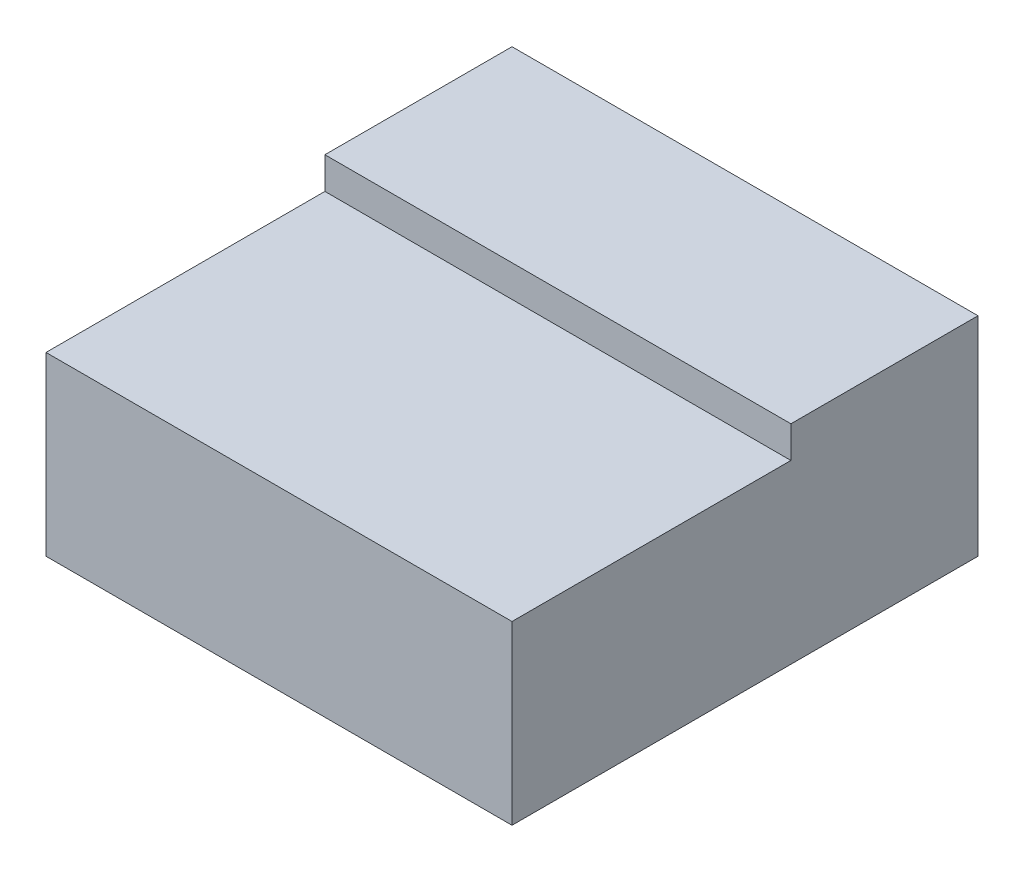
SolidWorks part; units mm, degrees
material "Copper"
ref_plane "Front" through (0, 0, 0) normal (0, 0, 1) x (1, 0, 0)
ref_plane "Top" through (0, 0, 0) normal (0, 1, 0) x (1, 0, 0)
ref_plane "Right" through (0, 0, 0) normal (1, 0, 0) x (0, 0, -1)
sketch "Sketch3" plane through (0, 0, 0) normal (1, 0, 0) x (0, 0, -1)
  line L1 (0, 0) -> (13.2, 0)
  line L2 (0, 0) -> (0, 5)
  line L3 (0, 5) -> (7.9, 5)
  line L4 (13.2, 0) -> (13.2, 5)
  line L6 (13.2, 5) -> (13.2, 5.9)
  line L7 (13.2, 5.9) -> (7.9, 5.9)
  line L8 (7.9, 5) -> (7.9, 5.9)
  point P8 (8.738, 5)
  dimension "D1" = 5
  dimension "D2" = 13.2
  dimension "D3" = 0.9
  dimension "D4" = 5.3
extrude "Boss-Extrude1" add sketch "Sketch3" along normal blind 13.2
hole_wizard "Ø1.5mm Dowel Hole1" positions "Sketch8" profile "Sketch7" hole size "Ø1.5" standard "ANSI Metric"
sketch "Sketch8" plane through (0, 0, -13.2) normal (0, 0, -1) x (-1, 0, 0)
  point P1 (-3.6, 2.95)
sketch "Sketch7" plane through (3.6, 2.95, -13.2) normal (1, 0, 0) x (0, 1, 0)
  line L0 (0, 0) -> (0, 6.4506)
  line L1 (0, 6.4506) -> (0.75, 6)
  line L2 (0.75, 6) -> (0.75, 0)
  line L5 (0.75, 0) -> (0, 0)
  line L10 (0, 6.4506) -> (-0.75, 6) construction
  line L11 (0, -6.35) -> (0, 107.95) construction
  dimension "Hole Dia." = 1.5
  dimension "Hole Depth" = 6
  dimension "Drill Angle" = 118
hole_wizard "Ø1.5mm Dowel Hole7" positions "Sketch20" profile "Sketch19" hole size "Ø1.5" standard "ANSI Metric"
sketch "Sketch20" plane through (0, 0, -13.2) normal (0, 0, -1) x (-1, 0, 0)
  point P0 (-9.6, 2.95)
  point P2 (-9.6, 2.95)
sketch "Sketch19" plane through (9.6, 2.95, -13.2) normal (1, 0, 0) x (0, 1, 0)
  line L0 (0, 0) -> (0, 6.4506)
  line L1 (0, 6.4506) -> (0.75, 6)
  line L2 (0.75, 6) -> (0.75, 0)
  line L5 (0.75, 0) -> (0, 0)
  line L10 (0, 6.4506) -> (-0.75, 6) construction
  line L11 (0, -6.35) -> (0, 107.95) construction
  dimension "Hole Dia." = 1.5
  dimension "Hole Depth" = 6
  dimension "Drill Angle" = 118
